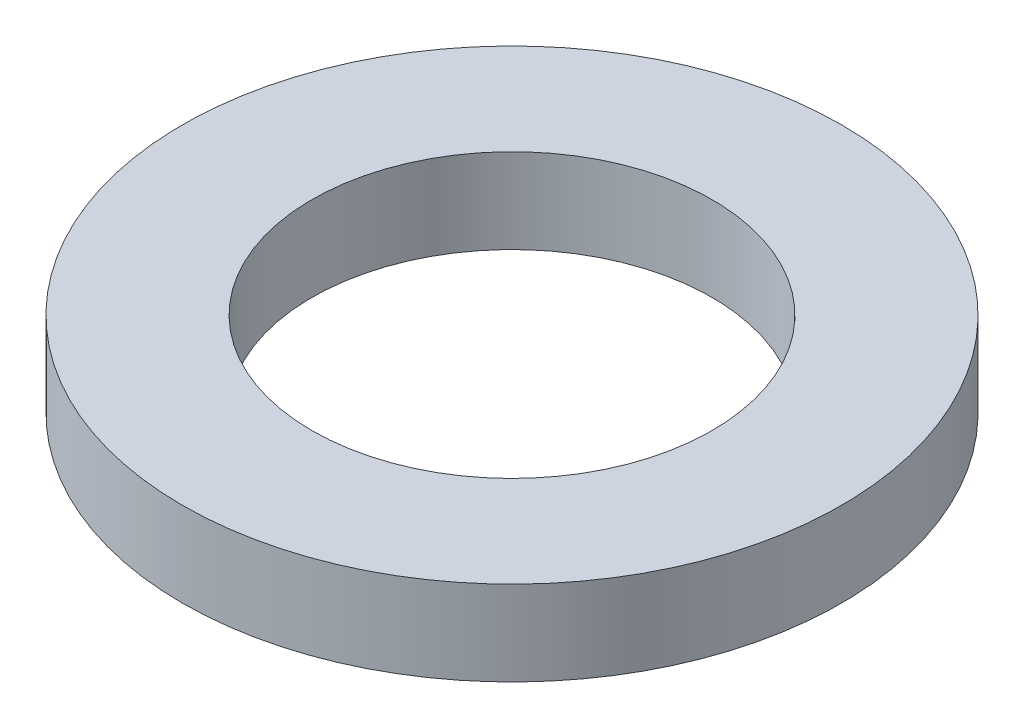
SolidWorks part; units mm, degrees
material "ABS"
ref_plane "Front Plane" through (0, 0, 0) normal (0, 0, 1) x (1, 0, 0)
ref_plane "Top Plane" through (0, 0, 0) normal (0, 1, 0) x (1, 0, 0)
ref_plane "Right Plane" through (0, 0, 0) normal (1, 0, 0) x (0, 0, -1)
sketch "Sketch1" plane through (0, 0, 0) normal (0, 1, 0) x (1, 0, 0)
  circle A0 centre (0, 0) radius 4.25
  circle A1 centre (0, 0) radius 7
  dimension "D1" = 8.5
  dimension "D2" = 14
extrude "Boss-Extrude1" add sketch "Sketch1" along normal blind 1.8
